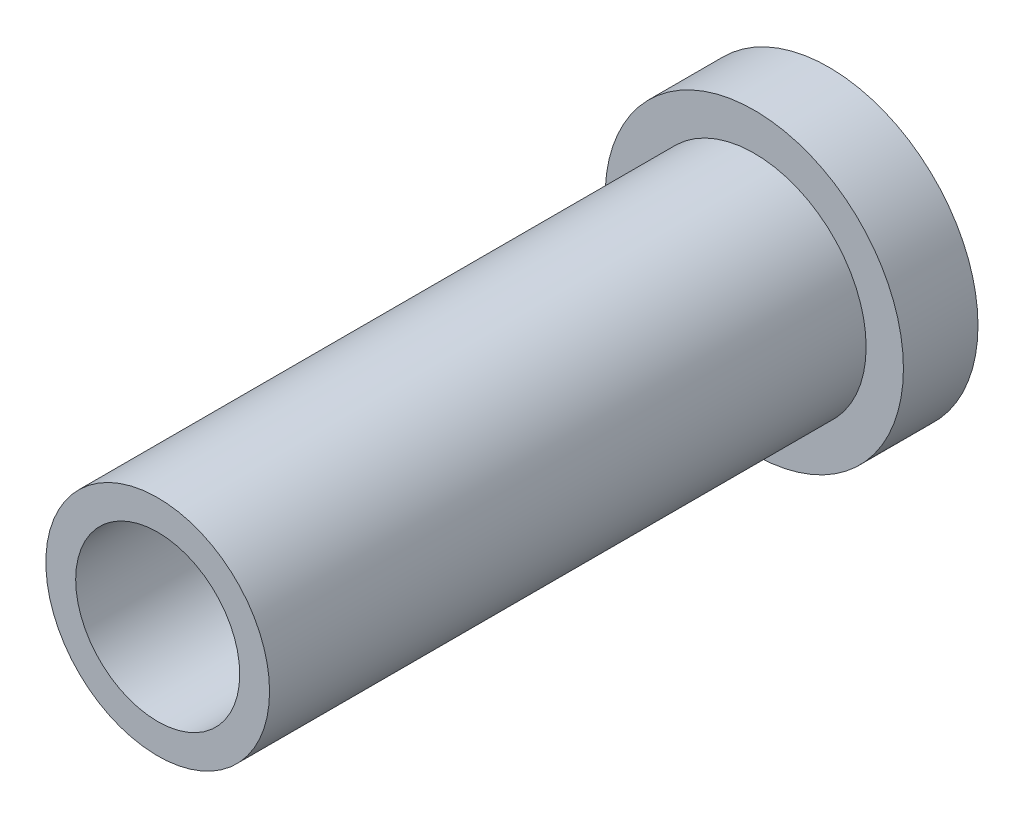
SolidWorks part; units mm, degrees
ref_plane "Front Plane" through (0, 0, 0) normal (0, 0, 1) x (1, 0, 0)
ref_plane "Top Plane" through (0, 0, 0) normal (0, 1, 0) x (1, 0, 0)
ref_plane "Right Plane" through (0, 0, 0) normal (1, 0, 0) x (0, 0, -1)
sketch "Sketch1" plane through (0, 0, 0) normal (0, 0, 1) x (1, 0, 0)
  circle A0 centre (0, 0) radius 10
  dimension "D1" = 20
extrude "Boss-Extrude1" add sketch "Sketch1" along normal blind 5
sketch "Sketch2" plane through (0, 0, 5) normal (0, 0, 1) x (1, 0, 0)
  circle A0 centre (0, 0) radius 7.5
  dimension "D1" = 15
extrude "Boss-Extrude2" add sketch "Sketch2" along normal blind 40
sketch "Sketch4" plane through (0, 0, 0) normal (0, 0, -1) x (-1, 0, 0)
  circle A0 centre (0, 0) radius 5.5
  dimension "D1" = 11
extrude "Cut-Extrude1" cut sketch "Sketch4" against normal up to surface (45 mm away) up to face at (7.5, 0, 45)
